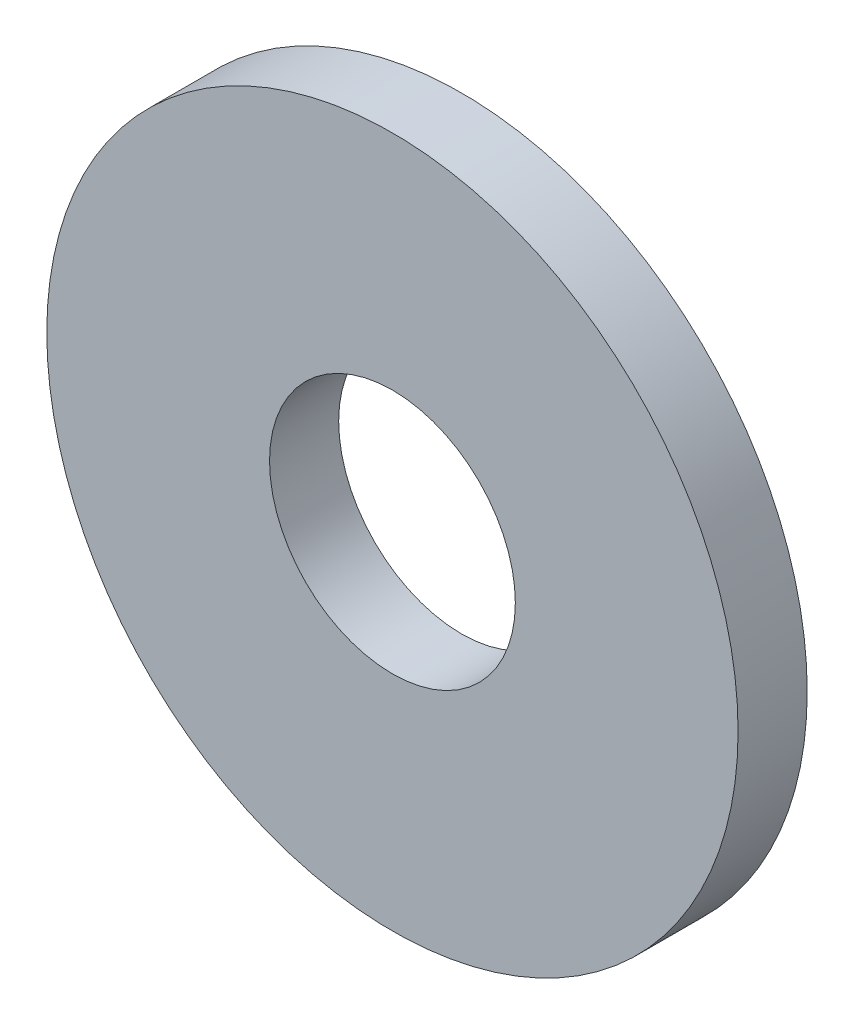
SolidWorks part; units mm, degrees
ref_plane "Front Plane" through (0, 0, 0) normal (0, 0, 1) x (1, 0, 0)
ref_plane "Top Plane" through (0, 0, 0) normal (0, 1, 0) x (1, 0, 0)
ref_plane "Right Plane" through (0, 0, 0) normal (1, 0, 0) x (0, 0, -1)
sketch "Sketch1" plane through (0, 0, 0) normal (0, 0, 1) x (1, 0, 0)
  circle A0 centre (0, 0) radius 4.5
  circle A1 centre (0, 0) radius 1.6
  dimension "OD" = 9
  dimension "ID1" = 3.2
extrude "Boss-Extrude1" add sketch "Sketch1" along normal blind 0.9
